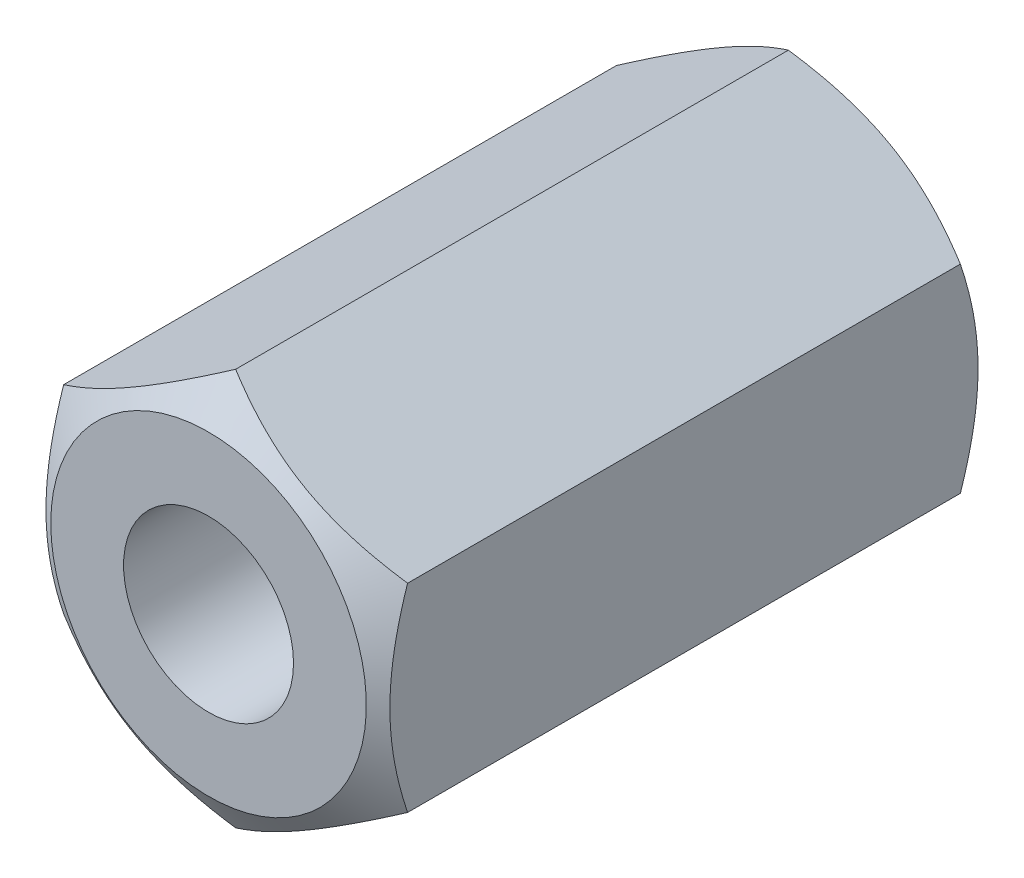
SolidWorks part; units mm, degrees
ref_plane "Front Plane" through (0, 0, 0) normal (0, 0, 1) x (1, 0, 0)
ref_plane "Top Plane" through (0, 0, 0) normal (0, 1, 0) x (1, 0, 0)
ref_plane "Right Plane" through (0, 0, 0) normal (1, 0, 0) x (0, 0, -1)
sketch "Sketch1" plane through (0, 0, 0) normal (0, 0, 1) x (1, 0, 0)
  line L1 (0, 9.815) -> (-8.5, 4.9075)
  line L2 (-8.5, 4.9075) -> (-8.5, -4.9075)
  line L3 (-8.5, -4.9075) -> (0, -9.815)
  line L4 (0, -9.815) -> (8.5, -4.9075)
  line L5 (8.5, -4.9075) -> (8.5, 4.9075)
  line L6 (8.5, 4.9075) -> (0, 9.815)
  circle A0 centre (0, 0) radius 8.5 construction
  dimension "D1" = 17
extrude "Boss-Extrude1" add sketch "Sketch1" along normal blind 30
sketch "Sketch2" plane through (0, 0, 30) normal (0, 0, 1) x (1, 0, 0)
  circle A0 centre (0, 0) radius 4.2
  dimension "D1" = 8.4
extrude "Cut-Extrude1" cut sketch "Sketch2" against normal through all
sketch "Sketch3" plane through (0, 0, 0) normal (1, 0, 0) x (0, 0, -1)
  line L0 (-15, 13.1115) -> (-15, -13.4151) construction
  line L1 (5.8721, 0) -> (-35.3029, 0) construction
  line L2 (-28.6617, 9.815) -> (-30, 7.7986)
  line L3 (-30, 9.815) -> (0, 9.815) construction
  line L4 (-30, 7.7986) -> (-30, 9.815)
  line L5 (-30, 9.815) -> (-28.6617, 9.815)
  line L6 (0, 7.7986) -> (0, 9.815)
  line L7 (0, 9.815) -> (-1.3383, 9.815)
  line L8 (-1.3383, 9.815) -> (0, 7.7986)
revolve "Cut-Revolve1" cut sketch "Sketch3" angle 360 about L1
